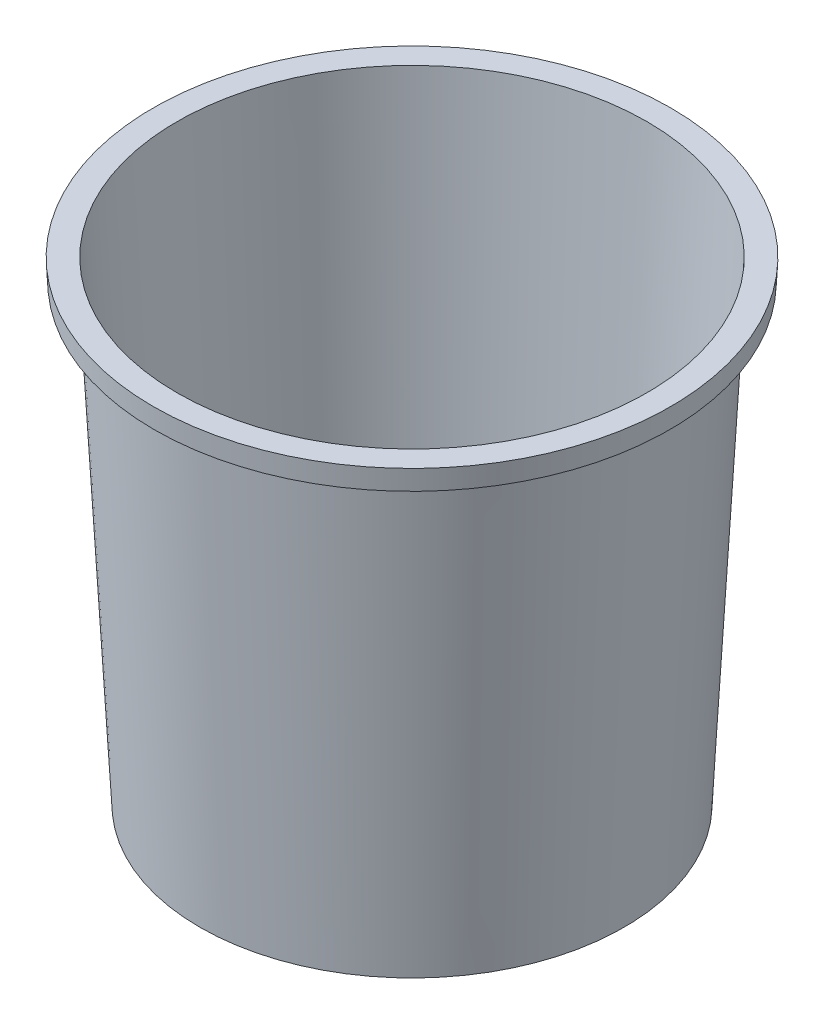
SolidWorks part; units mm, degrees
ref_plane "Front Plane" through (0, 0, 0) normal (0, 0, 1) x (1, 0, 0)
ref_plane "Top Plane" through (0, 0, 0) normal (0, 1, 0) x (1, 0, 0)
ref_plane "Right Plane" through (0, 0, 0) normal (1, 0, 0) x (0, 0, -1)
sketch "Sketch1" plane through (0, 0, 0) normal (0, 1, 0) x (1, 0, 0)
  circle A0 centre (0, 0) radius 102.9
extrude "Boss-Extrude1" add sketch "Sketch1" along normal blind 230 draft 3 contours A0 draft outward yes
shell "Shell2" thickness 1
ref_axis "Axis1" through (0, 230, 0) along (0, -1, 0)
sketch "Sketch4" plane through (0, 0, 0) normal (0, 0, 1) x (1, 0, 0)
  line L0 (114.9538, 230) -> (125.4779, 230)
  line L1 (125.4779, 230) -> (124.9538, 220)
  line L2 (124.9538, 220) -> (122.8491, 220)
  line L3 (122.8491, 220) -> (123.2685, 228.0027)
  line L4 (123.2685, 228.0027) -> (114.8491, 228.0027)
  line L5 (102.9, 0) -> (114.9538, 230) construction
  line L6 (114.8491, 228.0027) -> (114.9538, 230)
revolve "Revolve2" add sketch "Sketch4" angle 360 about axis through (0, 230, 0) along (0, -1, 0)
